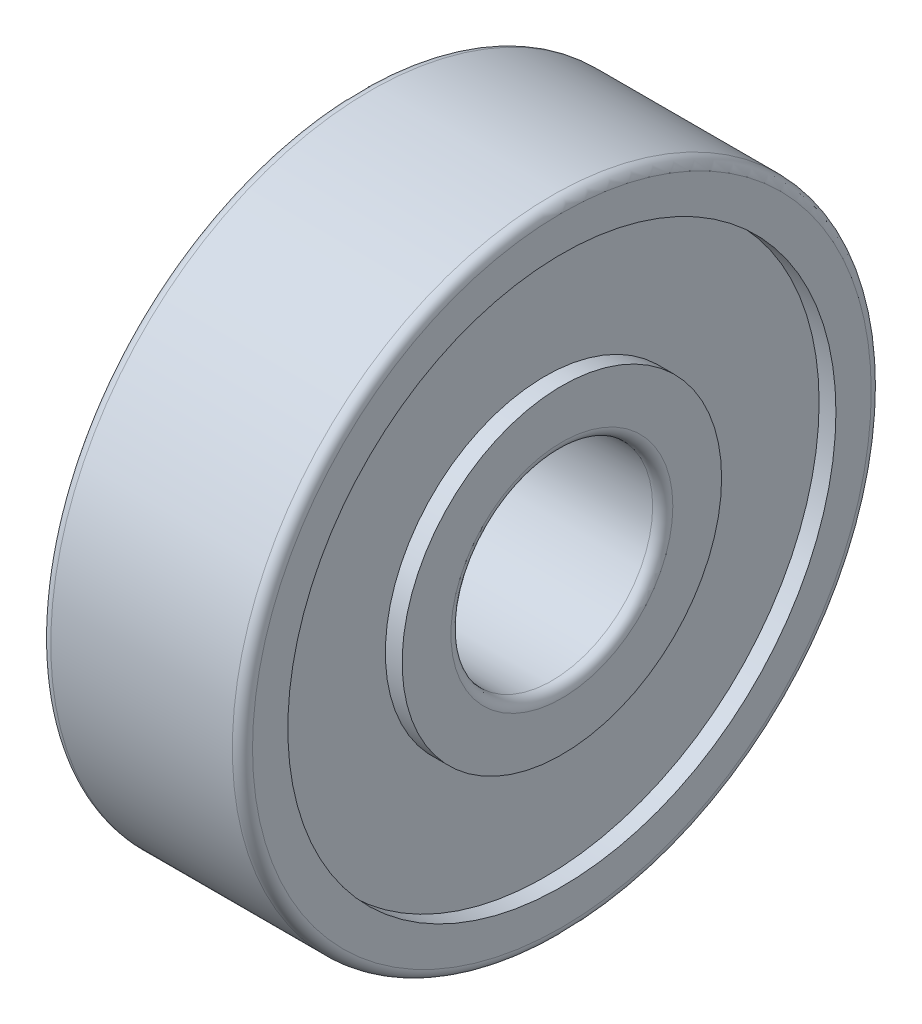
SolidWorks part; units mm, degrees
ref_plane "Front Plane" through (0, 0, 0) normal (0, 0, 1) x (1, 0, 0)
ref_plane "Top Plane" through (0, 0, 0) normal (0, 1, 0) x (1, 0, 0)
ref_plane "Right Plane" through (0, 0, 0) normal (1, 0, 0) x (0, 0, -1)
sketch "Sketch1" plane through (0, 0, 0) normal (0, 0, 1) x (1, 0, 0)
  line L0 (0, 4.75) -> (0, 3.3)
  line L1 (0.3, 3) -> (5.7, 3)
  line L2 (6, 3.3) -> (6, 4.75)
  line L3 (6, 4.75) -> (5.5, 4.75)
  line L4 (5.5, 4.75) -> (5.5, 8.15)
  line L5 (5.5, 8.15) -> (6, 8.15)
  line L6 (6, 8.15) -> (6, 9.2)
  line L7 (5.7, 9.5) -> (0.3, 9.5)
  line L8 (0, 9.2) -> (0, 8.15)
  line L9 (0, 8.15) -> (0.5, 8.15)
  line L10 (0.5, 8.15) -> (0.5, 4.75)
  line L11 (0.5, 4.75) -> (0, 4.75)
  line L12 (-0.0014, 0) -> (6.0014, 0) construction
  arc A0 (0, 3.3) -> (0.3, 3) centre (0.3, 3.3) ccw
  arc A1 (5.7, 3) -> (6, 3.3) centre (5.7, 3.3) ccw
  arc A2 (6, 9.2) -> (5.7, 9.5) centre (5.7, 9.2) ccw
  arc A3 (0.3, 9.5) -> (0, 9.2) centre (0.3, 9.2) ccw
revolve "Revolve1" add sketch "Sketch1" angle 360 about L12
